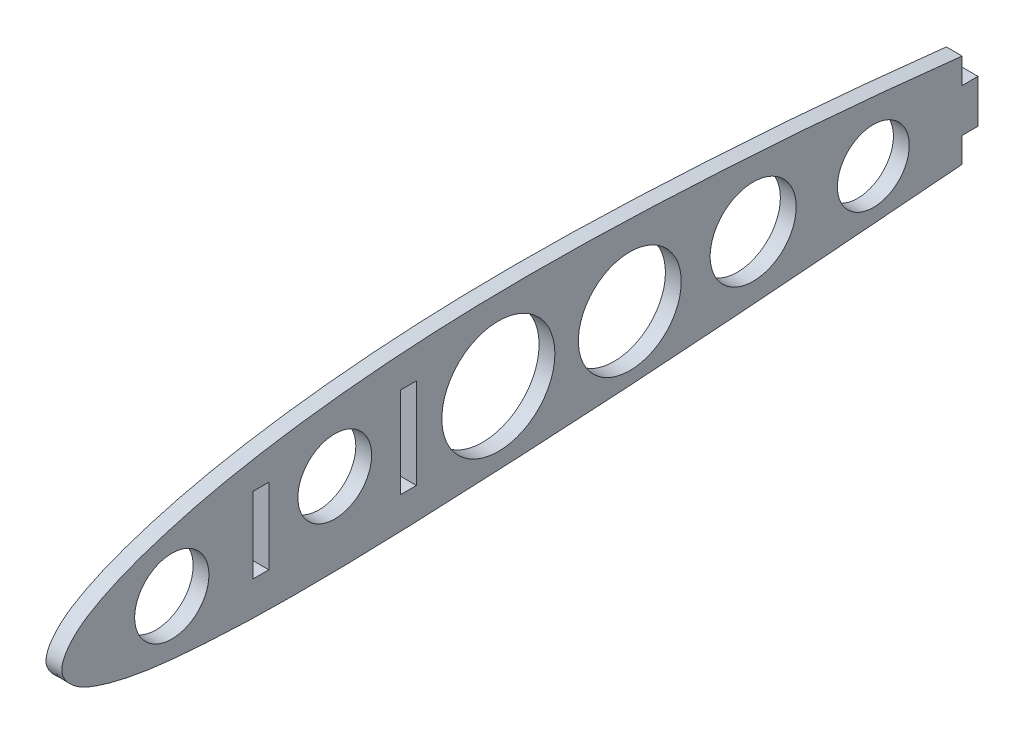
SolidWorks part; units mm, degrees
ref_plane "Front Plane" through (0, 0, 0) normal (0, 0, 1) x (1, 0, 0)
ref_plane "Top Plane" through (0, 0, 0) normal (0, 1, 0) x (1, 0, 0)
ref_plane "Right Plane" through (0, 0, 0) normal (1, 0, 0) x (0, 0, -1)
sketch "Sketch1" plane through (0, 0, 0) normal (1, 0, 0) x (0, 0, -1)
  line L0 (268.7968, 35.6725) -> (268.8089, 35.0387) construction
  line L1 (268.8029, 35.3556) -> (25, 31.1) construction
  line L2 (25, 31.1) -> (25, 53.7976) construction
  line L3 (25, 31.1) -> (85.95, 32.1639) construction
  line L4 (85.95, 32.1639) -> (85.95, 50.6064) construction
  line L5 (85.95, 32.1639) -> (85.95, 21.5874) construction
  line L6 (268.8089, 35.0387) -> (271.1066, 35.2448)
  line L7 (271.1066, 35.2448) -> (268.7968, 35.6725)
  line L8 (0, 0) -> (-220.2779, 0) construction
  spline S0 degree 3 poles (268.7968, 35.6725) (264.7203, 36.4275) (256.5779, 37.9354) (240.2845, 40.6711) (219.915, 43.6583) (195.4661, 46.686) (171.0322, 49.1341) (146.6025, 50.8024) (122.1915, 51.7827) (101.8429, 51.6405) (85.5966, 50.6585) (73.411, 49.4403) (61.2209, 47.6462) (51.0876, 45.5297) (43.0214, 43.1997) (36.9122, 41.1046) (31.7482, 38.7007) (27.3092, 35.8208) (23.4836, 30.9136) (27.6334, 26.743) (32.0784, 24.8893) (37.2912, 23.5162) (43.4378, 22.5774) (51.5949, 21.8315) (61.7689, 21.3315) (73.9746, 21.2854) (86.1656, 21.5558) (102.4123, 22.2234) (122.7188, 23.255) (147.0769, 24.8418) (171.4216, 26.7652) (195.7693, 28.7462) (220.1208, 30.7458) (240.4045, 32.5467) (256.6373, 33.947) (264.7515, 34.6748) (268.8089, 35.0387) knots 0 0 0 0 0.025012 0.049959 0.099673 0.149206 0.198581 0.247805 0.296917 0.345953 0.370492 0.395091 0.419815 0.444799 0.45749 0.470406 0.483879 0.491264 0.503459 0.513609 0.520451 0.533235 0.545691 0.558032 0.582609 0.607135 0.631652 0.656174 0.705234 0.75432 0.803437 0.852566 0.901701 0.950849 0.975423 1 1 1 1
  dimension "D1" = 243.84
  dimension "D2" = 60.95
  dimension "D3" = 29.019
  dimension "D4" = 1
  dimension "D5" = 25
  dimension "D6" = 31.1
extrude "Boss-Extrude1" add sketch "Sketch1" along normal blind 3
sketch "Sketch2" plane through (3, 0, 0) normal (1, 0, 0) x (0, 0, -1)
  line L0 (25, 31.1) -> (25, 64.8318) construction
  line L1 (198.85, 69.3791) -> (273.6913, 69.3791)
  line L2 (198.85, 69.3791) -> (198.85, 3.0641)
  line L3 (198.85, 3.0641) -> (273.6913, 3.0641)
  line L4 (273.6913, 69.3791) -> (273.6913, 3.0641)
  spline S0 degree 3 poles (268.7968, 35.6725) (264.7203, 36.4275) (256.5779, 37.9354) (240.2845, 40.6711) (219.915, 43.6583) (195.4661, 46.686) (171.0322, 49.1341) (146.6025, 50.8024) (122.1915, 51.7827) (101.8429, 51.6405) (85.5966, 50.6585) (73.411, 49.4403) (61.2209, 47.6462) (51.0876, 45.5297) (43.0214, 43.1997) (36.9122, 41.1046) (31.7482, 38.7007) (27.3092, 35.8208) (23.4836, 30.9136) (27.6334, 26.743) (32.0784, 24.8893) (37.2912, 23.5162) (43.4378, 22.5774) (51.5949, 21.8315) (61.7689, 21.3315) (73.9746, 21.2854) (86.1656, 21.5558) (102.4123, 22.2234) (122.7188, 23.255) (147.0769, 24.8418) (171.4216, 26.7652) (195.7693, 28.7462) (220.1208, 30.7458) (240.4045, 32.5467) (256.6373, 33.947) (264.7515, 34.6748) (268.8089, 35.0387) knots 0 0 0 0 0.025012 0.049959 0.099673 0.149206 0.198581 0.247805 0.296917 0.345953 0.370492 0.395091 0.419815 0.444799 0.45749 0.470406 0.483879 0.491264 0.503459 0.513609 0.520451 0.533235 0.545691 0.558032 0.582609 0.607135 0.631652 0.656174 0.705234 0.75432 0.803437 0.852566 0.901701 0.950849 0.975423 1 1 1 1 construction
  dimension "D1" = 173.85
extrude "Cut-Extrude1" cut sketch "Sketch2" against normal blind 3
sketch "Sketch3" plane through (3, 0, 0) normal (1, 0, 0) x (0, 0, -1)
  line L0 (25, 31.1) -> (25, 53.0277) construction
  line L1 (76.79, 36.9903) -> (76.79, 49.7403) construction
  line L2 (62.79, 42.2942) -> (62.79, 47.7942) construction
  line L3 (61.29, 42.2942) -> (64.29, 42.2942)
  line L4 (61.29, 42.2942) -> (61.29, 27.8987)
  line L5 (61.29, 27.8987) -> (64.29, 27.8987)
  line L6 (64.29, 42.2942) -> (64.29, 27.8987)
  line L7 (89.29, 44.9516) -> (92.29, 44.9516)
  line L8 (89.29, 44.9516) -> (89.29, 27.7557)
  line L9 (89.29, 27.7557) -> (92.29, 27.7557)
  line L10 (92.29, 44.9516) -> (92.29, 27.7557)
  line L11 (62.79, 27.8987) -> (62.79, 21.3987) construction
  line L12 (90.79, 44.9516) -> (90.79, 50.9516) construction
  line L13 (90.79, 27.7557) -> (90.79, 21.7557) construction
  circle A0 centre (76.79, 36.9903) radius 7
  spline S0 degree 3 poles (198.85, 46.2051) (197.7099, 46.3365) (188.4378, 47.3901) (171.0322, 49.1341) (146.6025, 50.8024) (122.1915, 51.7827) (101.8429, 51.6405) (85.5966, 50.6585) (73.411, 49.4403) (61.2209, 47.6462) (51.0876, 45.5297) (43.0214, 43.1997) (36.9122, 41.1046) (31.7482, 38.7007) (27.3092, 35.8208) (23.4836, 30.9136) (27.6334, 26.743) (32.0784, 24.8893) (37.2912, 23.5162) (43.4378, 22.5774) (51.5949, 21.8315) (61.7689, 21.3315) (73.9746, 21.2854) (86.1656, 21.5558) (102.4123, 22.2234) (122.7188, 23.255) (147.0769, 24.8418) (171.4216, 26.7652) (188.6794, 28.1693) (197.8227, 28.9171) (198.85, 29.0012) knots 0.142282 0.142282 0.142282 0.142282 0.149206 0.198581 0.247805 0.296917 0.345953 0.370492 0.395091 0.419815 0.444799 0.45749 0.470406 0.483879 0.491264 0.503459 0.513609 0.520451 0.533235 0.545691 0.558032 0.582609 0.607135 0.631652 0.656174 0.705234 0.75432 0.803437 0.852566 0.858785 0.858785 0.858785 0.858785 construction
  dimension "D1" = 14
  dimension "D2" = 51.79
  dimension "D3" = 12.75
  dimension "D4" = 25
  dimension "D5" = 3
  dimension "D6" = 12.5
  dimension "D7" = 5.5
  dimension "D8" = 6.5
  dimension "D9" = 6
  dimension "D10" = 6
extrude "Cut-Extrude2" cut sketch "Sketch3" against normal blind 3
sketch "Sketch4" plane through (3, 0, 0) normal (1, 0, 0) x (0, 0, -1)
  circle A0 centre (45.873, 32.77) radius 7.0449
  circle A1 centre (107.8399, 36.2891) radius 10.7245
  circle A2 centre (132.7796, 36.1361) radius 9.7588
  circle A3 centre (156.1893, 37.5131) radius 8.161
  circle A4 centre (178.987, 36.9011) radius 6.8169
extrude "Cut-Extrude3" cut sketch "Sketch4" against normal blind 10
sketch "Sketch5" plane through (3, 0, 0) normal (1, 0, 0) x (0, 0, -1)
  line L0 (198.85, 46.2051) -> (198.85, 29.0012) construction
  line L1 (198.85, 41.7051) -> (195.85, 41.7051)
  line L2 (198.85, 41.7051) -> (198.85, 50.9589)
  line L3 (198.85, 50.9589) -> (195.85, 50.9589)
  line L4 (195.85, 41.7051) -> (195.85, 50.9589)
  line L6 (198.85, 33.5012) -> (195.85, 33.5012)
  line L7 (198.85, 33.5012) -> (198.85, 22.288)
  line L8 (198.85, 22.288) -> (195.85, 22.288)
  line L9 (195.85, 33.5012) -> (195.85, 22.288)
  dimension "D1" = 3
  dimension "D2" = 4.5
  dimension "D3" = 4.5
extrude "Cut-Extrude4" cut sketch "Sketch5" against normal blind 10
